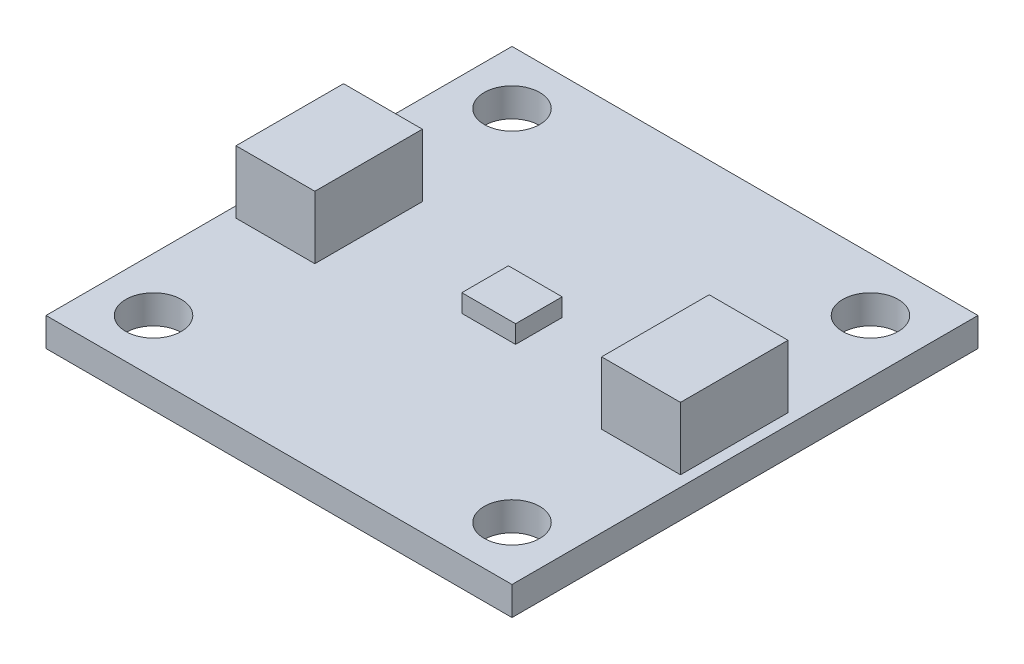
SolidWorks part; units mm, degrees
ref_plane "Front Plane" through (0, 0, 0) normal (0, 0, 1) x (1, 0, 0)
ref_plane "Top Plane" through (0, 0, 0) normal (0, 1, 0) x (1, 0, 0)
ref_plane "Right Plane" through (0, 0, 0) normal (1, 0, 0) x (0, 0, -1)
sketch "Sketch1" plane through (0, 0, 0) normal (0, 1, 0) x (1, 0, 0)
  line L1 (-13, -13) -> (13, -13)
  line L2 (-13, -13) -> (-13, 13)
  line L3 (-13, 13) -> (13, 13)
  line L4 (13, -13) -> (13, 13)
  line L5 (-13, -13) -> (13, 13) construction
  line L6 (-13, 13) -> (13, -13) construction
  line L7 (10, -10) -> (-10, -10) construction
  line L8 (10, -10) -> (10, 10) construction
  line L9 (10, 10) -> (-10, 10) construction
  line L10 (-10, -10) -> (-10, 10) construction
  line L11 (10, -10) -> (-10, 10) construction
  line L12 (10, 10) -> (-10, -10) construction
  circle A0 centre (-10, 10) radius 1.55
  circle A1 centre (10, 10) radius 1.55
  circle A2 centre (10, -10) radius 1.55
  circle A3 centre (-10, -10) radius 1.55
  point P0 (0, 0)
  point P6 (0, 0)
  dimension "D1" = 3.1
  dimension "D2" = 26
  dimension "D3" = 20
extrude "Boss-Extrude1" add sketch "Sketch1" along normal blind 1.6
sketch "Sketch2" plane through (0, 1.6, 0) normal (0, 1, 0) x (1, 0, 0)
  line L0 (-13, 0) -> (13, 0) construction
  line L1 (-13, 13) -> (-13, -13) construction
  line L2 (13, -13) -> (13, 13) construction
  line L4 (-8, -3) -> (-12.4, -3)
  line L5 (-8, -3) -> (-8, 3)
  line L6 (-8, 3) -> (-12.4, 3)
  line L7 (-12.4, -3) -> (-12.4, 3)
  line L8 (-8, -3) -> (-12.4, 3) construction
  line L9 (-8, 3) -> (-12.4, -3) construction
  line L10 (12.4, -3) -> (8, -3)
  line L11 (12.4, -3) -> (12.4, 3)
  line L12 (12.4, 3) -> (8, 3)
  line L13 (8, -3) -> (8, 3)
  line L14 (12.4, -3) -> (8, 3) construction
  line L15 (12.4, 3) -> (8, -3) construction
  point P6 (-10.2, 0)
  point P11 (10.2, 0)
  dimension "D1" = 4.4
  dimension "D2" = 6
  dimension "D3" = 0.6
  dimension "D4" = 0.6
extrude "Boss-Extrude2" add sketch "Sketch2" along normal blind 3.5
sketch "Sketch3" plane through (0, 1.6, 0) normal (0, 1, 0) x (1, 0, 0)
  line L1 (-1.5, -1.3) -> (1.5, -1.3)
  line L2 (-1.5, -1.3) -> (-1.5, 1.3)
  line L3 (-1.5, 1.3) -> (1.5, 1.3)
  line L4 (1.5, -1.3) -> (1.5, 1.3)
  line L5 (-1.5, -1.3) -> (1.5, 1.3) construction
  line L6 (-1.5, 1.3) -> (1.5, -1.3) construction
  point P0 (0, 0)
  dimension "D1" = 3
  dimension "D2" = 2.6
extrude "Boss-Extrude3" add sketch "Sketch3" along normal blind 1
